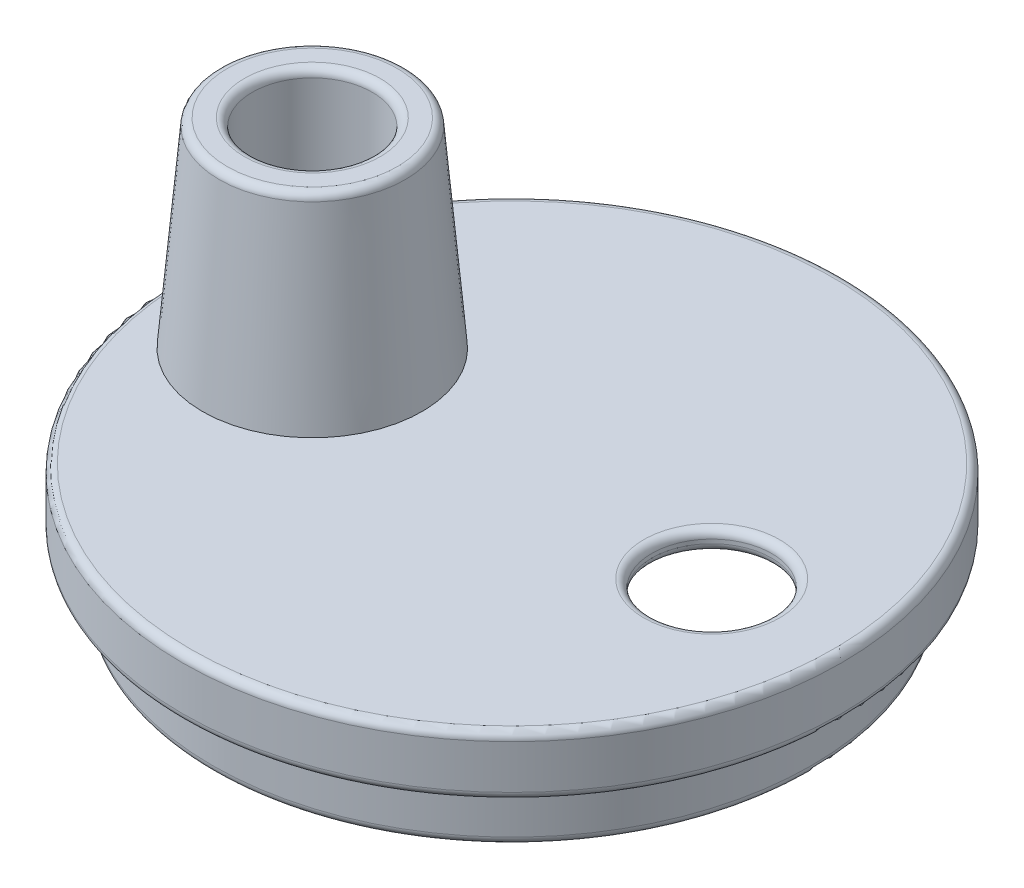
SolidWorks part; units mm, degrees
ref_plane "Front Plane" through (0, 0, 0) normal (0, 0, 1) x (1, 0, 0)
ref_plane "Top Plane" through (0, 0, 0) normal (0, 1, 0) x (1, 0, 0)
ref_plane "Right Plane" through (0, 0, 0) normal (1, 0, 0) x (0, 0, -1)
sketch "Sketch1" plane through (0, 0, 0) normal (1, 0, 0) x (0, 0, -1)
  line L0 (-8.25, -1.5) -> (-7.5, -1.5)
  line L1 (0, 0) -> (-8.25, 0)
  line L2 (0, 0) -> (0, -3) construction
  line L3 (0, -0.5) -> (-7.75, -0.5)
  line L4 (-8.25, 0) -> (-8.25, -1.5)
  line L5 (-7.75, -0.5) -> (-7.75, -1)
  line L6 (-7.75, -1) -> (-7, -1)
  line L7 (0, -3) -> (-7.5, -3) construction
  line L8 (-7.5, -1.5) -> (-7.5, -3)
  line L9 (-7, -1) -> (-7, -3)
  line L10 (0, -0.5) -> (0, 0)
  line L11 (-7, -3) -> (-7.5, -3)
  dimension "D1" = 8.25
  dimension "D2" = 1.5
  dimension "D3" = 7.5
  dimension "D4" = 3
  dimension "D5" = 0.5
revolve "Revolve1" add sketch "Sketch1" angle 360 about L2
sketch "Sketch2" plane through (0, 0, 0) normal (0, 1, 0) x (1, 0, 0)
  line L0 (0, 8.25) -> (0, -8.25) construction
  line L1 (-8.25, 0) -> (8.25, 0) construction
  circle A0 centre (0, 0) radius 8.25 construction
  circle A1 centre (5, 0) radius 1.5
  circle A2 centre (-5, 0) radius 1.5
  dimension "D1" = 3
  dimension "D2" = 5
extrude "Cut-Extrude1" cut sketch "Sketch2" against normal up to next
sketch "Sketch3" plane through (0, 0, 0) normal (0, 1, 0) x (1, 0, 0)
  line L0 (0, 0) -> (-5, 0) construction
  circle A0 centre (-5, 0) radius 1.5
  circle A1 centre (-5, 0) radius 2.75
  dimension "D2" = 3
  dimension "D3" = 5.5
  dimension "D1" = 5
extrude "Boss-Extrude1" add sketch "Sketch3" along normal blind 5
draft "Draft2" type of draft neutral plane draft angle 5 faces to draft 1 face at (-5, 5, 2.75) neutral plane through (0, 0, 0) neutral plane normal (0, 1, 0) parameters "D1"=5
fillet "Fillet1" radius 0.2 9 edges at (-5, -0.5, -1.5) (0, -3, 7) (0, -3, 7.5) (0, -1.5, 8.25) (5, -0.5, -1.5) (5, 0, 1.5) (-5, 5, 2.3126) (-5, 5, 1.5) (0, 0, 8.25)
